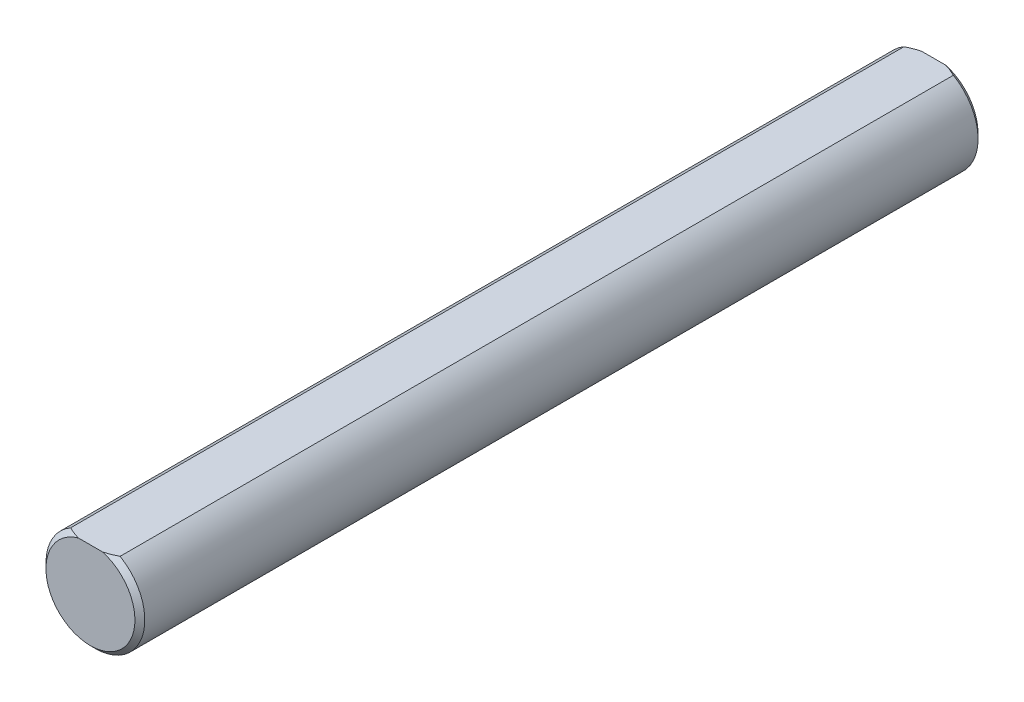
SolidWorks part; units mm, degrees
material "Plain Carbon Steel"
ref_plane "Front Plane" through (0, 0, 0) normal (0, 0, 1) x (1, 0, 0)
ref_plane "Top Plane" through (0, 0, 0) normal (0, 1, 0) x (1, 0, 0)
ref_plane "Right Plane" through (0, 0, 0) normal (1, 0, 0) x (0, 0, -1)
sketch "Sketch1" plane through (0, 0, 0) normal (0, 0, 1) x (1, 0, 0)
  line L0 (-1.5875, 2.7496) -> (1.5875, 2.7496) construction
  circle A1 centre (0, 0) radius 3.175 construction
  dimension "Diameter" = 6.35
  dimension "Flat Width" = 3.175
sketch "Sketch2" plane through (0, 0, 0) normal (1, 0, 0) x (0, 0, -1)
  line L0 (-27.08, 3.175) -> (27.08, 3.175) construction
  line L1 (0, 3.175) -> (0, -3.175) construction
  line L2 (0, 3.175) -> (0, -3.175) construction
  line L3 (-27.08, 3.175) -> (-27.08, -3.175) construction
  line L4 (-27.08, -3.175) -> (27.08, -3.175) construction
  point P2 (0, 3.175)
  point P3 (14.38, 3.175)
  point P4 (-14.38, 3.175)
  dimension "Length" = 54.16
  dimension "D2" = 12.7
  dimension "D1" = 12.7
  dimension "D-Profile Length" = 54.16
sketch "Sketch3" plane through (0, 0, 0) normal (0, 0, 1) x (1, 0, 0)
  circle A1 centre (0, 0) radius 3.175 construction
  circle A3 centre (0, 0) radius 3.175
extrude "Boss-Extrude2" add sketch "Sketch3" along normal up to vertex (27.08 mm away) and the other way up to vertex (27.08 mm away) up to point (0, 3.175, 27.08) other way up to point (0, 3.175, -27.08)
sketch "Sketch10" plane through (0, 0, 0) normal (0, 0, 1) x (1, 0, 0)
  line L0 (-1.5875, 2.7496) -> (1.5875, 2.7496)
  line L1 (0, 0) -> (0, 3.175) construction
  circle A0 centre (0, 0) radius 3.175 construction
  circle A1 centre (0, 0) radius 3.175 construction
  arc A2 (-1.5875, 2.7496) -> (1.5875, 2.7496) centre (0, 0) cw
extrude "Cut-Extrude5" cut sketch "Sketch10" against normal through all both and the other way through all
chamfer "Chamfer1" distance 0.3175 angle 45 4 edges at (0, -3.175, 27.08) (0, -3.175, -27.08) (0, 2.7496, -27.08) (0, 2.7496, 27.08)
equation "\"D1@Chamfer1\"= \"Diameter@Sketch1\" / 20"
equation "\"D1@Sketch2\"=\"Diameter@Sketch1\"*2"
equation "\"D2@Sketch2\"=\"D1@Sketch2\""
equation "\"D-Profile Length@Sketch2\"=\"Length@Sketch2\""
